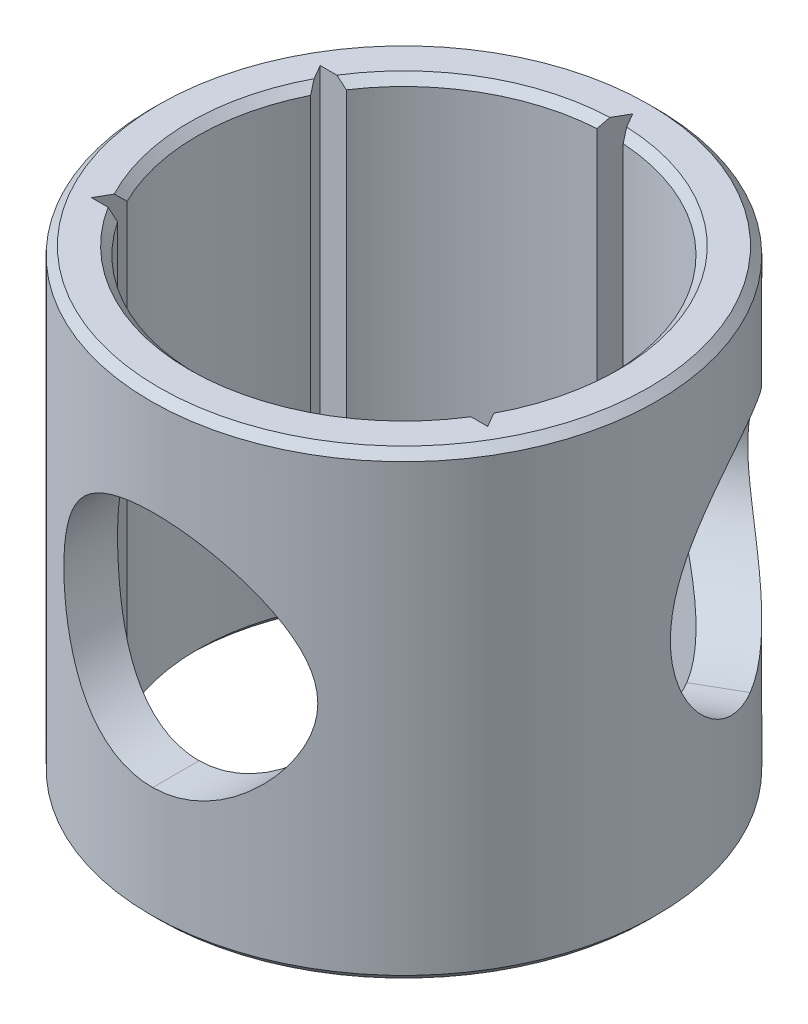
SolidWorks part; units mm, degrees
ref_plane "Ebene vorne" through (0, 0, 0) normal (0, 0, 1) x (1, 0, 0)
ref_plane "Ebene oben" through (0, 0, 0) normal (0, 1, 0) x (1, 0, 0)
ref_plane "Ebene rechts" through (0, 0, 0) normal (1, 0, 0) x (0, 0, -1)
sketch "Skizze1" plane through (0, 0, 0) normal (0, 1, 0) x (1, 0, 0)
  circle A0 centre (0, 0) radius 13
  circle A1 centre (0, 0) radius 15.925
  dimension "D1" = 26
  dimension "D2" = 31.85
extrude "Aufsatz-Linear austragen1" add sketch "Skizze1" along normal blind 29
sketch "Skizze2" plane through (0, 29, 0) normal (0, 1, 0) x (1, 0, 0)
  line L1 (0, 14.4) -> (-1.2124, 12.3)
  line L2 (-1.2124, 12.3) -> (1.2124, 12.3)
  line L3 (1.2124, 12.3) -> (0, 14.4)
  circle A0 centre (0, 13) radius 0.7 construction
  circle A1 centre (0, 0) radius 13 construction
  dimension "D1" = 1.4
extrude "Schnitt-Linear austragen1" cut sketch "Skizze2" against normal blind 30
pattern_circular "Kreismuster1" count 6 over 360 about axis through (0, 0, 0) along (0, 1, 0) skipping 3, 5 of "Schnitt-Linear austragen1"
sketch3d "3D-Skizze1"
  spline S0 degree 3 poles (-457.6373, -1653.7984, -975.9731) (-97.1864, -142.0144, -82.2273) (-28.6155, 28.5725, 16.7947) (2.1671, 22.2371, 12.8282) (2.6665, 22.0809, 12.7328) (3.606, 21.6883, 12.4992) (4.0502, 21.4519, 12.3611) (4.8934, 20.905, 12.0522) (5.2851, 20.5992, 11.884) (5.8276, 20.0999, 11.6224) (6.0012, 19.9264, 11.5335) (6.3344, 19.5649, 11.3539) (6.4946, 19.3761, 11.2628) (6.9484, 18.793, 10.9929) (7.2167, 18.3823, 10.8166) (7.6782, 17.5043, 10.494) (7.8731, 17.0307, 10.3462) (8.0761, 16.2899, 10.1874) (8.1293, 16.0372, 10.1448) (8.2016, 15.518, 10.0864) (8.2199, 15.2544, 10.0714) (8.2194, 14.7336, 10.0718) (8.2008, 14.4742, 10.0871) (8.1282, 13.9574, 10.1456) (8.0739, 13.7007, 10.1892) (7.9379, 13.2073, 10.2955) (7.8559, 12.9679, 10.3585) (7.6677, 12.5009, 10.4986) (7.5609, 12.2722, 10.576) (7.2118, 11.6092, 10.8199) (6.9431, 11.1997, 10.9962) (6.4929, 10.6219, 11.2638) (6.3348, 10.4355, 11.3537) (6.0022, 10.0747, 11.5329) (5.827, 9.8995, 11.6227) (5.2817, 9.3979, 11.8855) (4.8933, 9.0954, 12.052) (4.2697, 8.6903, 12.2808) (4.055, 8.5635, 12.3536) (3.6106, 8.3272, 12.4907) (3.3796, 8.2174, 12.5554) (2.6708, 7.9203, 12.732) (2.1818, 7.7668, 12.8258) (-21.2275, 2.9072, 15.8664) (-86.0881, 98.182, -39.1961) (1664.0012, 951.8719, -559.7226) knots -3.679496 -3.679496 -3.679496 -3.679496 0.0625 0.0625 0.125 0.125 0.1875 0.1875 0.25 0.25 0.28125 0.28125 0.3125 0.3125 0.375 0.375 0.4375 0.4375 0.46875 0.46875 0.5 0.5 0.53125 0.53125 0.5625 0.5625 0.59375 0.59375 0.625 0.625 0.6875 0.6875 0.71875 0.71875 0.75 0.75 0.8125 0.8125 0.84375 0.84375 0.875 0.875 0.9375 0.9375 3.759159 3.759159 3.759159 3.759159 only from (0.1111, 22.5, 12.9995) to (0.1111, 7.5, 12.9995) construction
  spline S1 degree 3 poles (0.1111, 22.5, 12.9995) (0.6393, 22.5, 12.995) (1.1557, 22.4452, 12.9586) (2.1671, 22.2371, 12.8282) (2.6665, 22.0809, 12.7328) (3.606, 21.6883, 12.4992) (4.0502, 21.4519, 12.3611) (4.8934, 20.905, 12.0522) (5.2851, 20.5992, 11.884) (5.8276, 20.0999, 11.6224) (6.0012, 19.9264, 11.5335) (6.3344, 19.5649, 11.3539) (6.4946, 19.3761, 11.2628) (6.9484, 18.793, 10.9929) (7.2167, 18.3823, 10.8166) (7.6782, 17.5043, 10.494) (7.8731, 17.0307, 10.3462) (8.0761, 16.2899, 10.1874) (8.1293, 16.0372, 10.1448) (8.2016, 15.518, 10.0864) (8.2199, 15.2544, 10.0714) (8.2194, 14.7336, 10.0718) (8.2008, 14.4742, 10.0871) (8.1282, 13.9574, 10.1456) (8.0739, 13.7007, 10.1892) (7.9379, 13.2073, 10.2955) (7.8559, 12.9679, 10.3585) (7.6677, 12.5009, 10.4986) (7.5609, 12.2722, 10.576) (7.2118, 11.6092, 10.8199) (6.9431, 11.1997, 10.9962) (6.4929, 10.6219, 11.2638) (6.3348, 10.4355, 11.3537) (6.0022, 10.0747, 11.5329) (5.827, 9.8995, 11.6227) (5.2817, 9.3979, 11.8855) (4.8933, 9.0954, 12.052) (4.2697, 8.6903, 12.2808) (4.055, 8.5635, 12.3536) (3.6106, 8.3272, 12.4907) (3.3796, 8.2174, 12.5554) (2.6708, 7.9203, 12.732) (2.1818, 7.7668, 12.8258) (1.1672, 7.5562, 12.9576) (0.6393, 7.5, 12.995) (0.1111, 7.5, 12.9995) knots 0 0 0 0 0.0625 0.0625 0.125 0.125 0.1875 0.1875 0.25 0.25 0.28125 0.28125 0.3125 0.3125 0.375 0.375 0.4375 0.4375 0.46875 0.46875 0.5 0.5 0.53125 0.53125 0.5625 0.5625 0.59375 0.59375 0.625 0.625 0.6875 0.6875 0.71875 0.71875 0.75 0.75 0.8125 0.8125 0.84375 0.84375 0.875 0.875 0.9375 0.9375 1 1 1 1
  spline S2 degree 3 poles (419.1015, 1299.7716, -1451.6243) (117.6658, 245.0229, -117.1146) (33.5692, 0.596, 16.6152) (-1.8468, 7.7441, 12.8773) (-2.3241, 7.8921, 12.7988) (-3.2185, 8.2722, 12.6036) (-3.6402, 8.5042, 12.4869) (-4.4351, 9.0532, 12.2272) (-4.798, 9.3633, 12.0875) (-5.2909, 9.8768, 11.8759) (-5.4469, 10.0564, 11.805) (-5.7423, 10.4328, 11.6642) (-5.8813, 10.6296, 11.5944) (-6.2658, 11.2344, 11.394) (-6.4819, 11.6606, 11.2706) (-6.7472, 12.3371, 11.1124) (-6.8261, 12.5701, 11.064) (-6.9613, 13.0431, 10.9794) (-7.0175, 13.2818, 10.9434) (-7.1527, 14.0042, 10.8559) (-7.1989, 14.4944, 10.8248) (-7.1994, 15.2434, 10.8244) (-7.1879, 15.4941, 10.8321) (-7.1425, 15.9872, 10.8621) (-7.0746, 16.475, 10.9068) (-6.9624, 16.9526, 10.9787) (-6.8276, 17.4251, 11.063) (-6.7487, 17.6588, 11.1115) (-6.483, 18.3373, 11.27) (-6.2663, 18.765, 11.3938) (-5.8802, 19.3721, 11.595) (-5.7408, 19.5692, 11.6649) (-5.4462, 19.9444, 11.8053) (-5.2906, 20.1235, 11.8761) (-4.7984, 20.6363, 12.0873) (-4.4352, 20.9467, 12.2272) (-3.6407, 21.4955, 12.4868) (-3.2201, 21.7268, 12.6031) (-2.5528, 22.0109, 12.7489) (-2.3242, 22.095, 12.7928) (-1.8541, 22.2411, 12.8693) (-1.6121, 22.3031, 12.902) (36.2667, 29.9756, 16.9146) (123.0672, -256.026, -139.4864) (372.8421, -1147.1035, -1560.664) knots -4.464251 -4.464251 -4.464251 -4.464251 0.0625 0.0625 0.125 0.125 0.1875 0.1875 0.25 0.25 0.28125 0.28125 0.3125 0.3125 0.375 0.375 0.40625 0.40625 0.4375 0.4375 0.5 0.5 0.53125 0.53125 0.5625 0.59375 0.59375 0.625 0.625 0.6875 0.6875 0.71875 0.71875 0.75 0.75 0.8125 0.8125 0.875 0.875 0.90625 0.90625 0.9375 0.9375 5.784955 5.784955 5.784955 5.784955 only from (0.1111, 7.5, 12.9995) to (0.1111, 22.5, 12.9995) construction
  spline S3 degree 3 poles (0.1111, 7.5, 12.9995) (-0.3904, 7.5, 13.0038) (-0.8821, 7.5494, 12.9791) (-1.8468, 7.7441, 12.8773) (-2.3241, 7.8921, 12.7988) (-3.2185, 8.2722, 12.6036) (-3.6402, 8.5042, 12.4869) (-4.4351, 9.0532, 12.2272) (-4.798, 9.3633, 12.0875) (-5.2909, 9.8768, 11.8759) (-5.4469, 10.0564, 11.805) (-5.7423, 10.4328, 11.6642) (-5.8813, 10.6296, 11.5944) (-6.2658, 11.2344, 11.394) (-6.4819, 11.6606, 11.2706) (-6.7472, 12.3371, 11.1124) (-6.8261, 12.5701, 11.064) (-6.9613, 13.0431, 10.9794) (-7.0175, 13.2818, 10.9434) (-7.1527, 14.0042, 10.8559) (-7.1989, 14.4944, 10.8248) (-7.1994, 15.2434, 10.8244) (-7.1879, 15.4941, 10.8321) (-7.1425, 15.9872, 10.8621) (-7.0746, 16.475, 10.9068) (-6.9624, 16.9526, 10.9787) (-6.8276, 17.4251, 11.063) (-6.7487, 17.6588, 11.1115) (-6.483, 18.3373, 11.27) (-6.2663, 18.765, 11.3938) (-5.8802, 19.3721, 11.595) (-5.7408, 19.5692, 11.6649) (-5.4462, 19.9444, 11.8053) (-5.2906, 20.1235, 11.8761) (-4.7984, 20.6363, 12.0873) (-4.4352, 20.9467, 12.2272) (-3.6407, 21.4955, 12.4868) (-3.2201, 21.7268, 12.6031) (-2.5528, 22.0109, 12.7489) (-2.3242, 22.095, 12.7928) (-1.8541, 22.2411, 12.8693) (-1.6121, 22.3031, 12.902) (-0.8842, 22.4505, 12.9791) (-0.3908, 22.5, 13.0038) (0.1111, 22.5, 12.9995) knots 0 0 0 0 0.0625 0.0625 0.125 0.125 0.1875 0.1875 0.25 0.25 0.28125 0.28125 0.3125 0.3125 0.375 0.375 0.40625 0.40625 0.4375 0.4375 0.5 0.5 0.53125 0.53125 0.5625 0.59375 0.59375 0.625 0.625 0.6875 0.6875 0.71875 0.71875 0.75 0.75 0.8125 0.8125 0.875 0.875 0.90625 0.90625 0.9375 0.9375 1 1 1 1
sketch "Skizze4" plane through (0, 0, 0) normal (0, 0, 1) x (1, 0, 0)
  spline S0 degree 3 poles (-518.1127, -1908.464) (-104.6424, -160.7971) (-30.2373, 28.9063) (2.1671, 22.2371) (2.6665, 22.0809) (3.606, 21.6883) (4.0502, 21.4519) (4.8934, 20.905) (5.2851, 20.5992) (5.8276, 20.0999) (6.0012, 19.9264) (6.3344, 19.5649) (6.4946, 19.3761) (6.9484, 18.793) (7.2167, 18.3823) (7.6782, 17.5043) (7.8731, 17.0307) (8.0761, 16.2899) (8.1293, 16.0372) (8.2016, 15.518) (8.2199, 15.2544) (8.2194, 14.7336) (8.2008, 14.4742) (8.1282, 13.9574) (8.0739, 13.7007) (7.9379, 13.2073) (7.8559, 12.9679) (7.6677, 12.5009) (7.5609, 12.2722) (7.2118, 11.6092) (6.9431, 11.1997) (6.4929, 10.6219) (6.3348, 10.4355) (6.0022, 10.0747) (5.827, 9.8995) (5.2817, 9.3979) (4.8933, 9.0954) (4.2697, 8.6903) (4.055, 8.5635) (3.6106, 8.3272) (3.3796, 8.2174) (2.6708, 7.9203) (2.1818, 7.7668) (-21.5542, 2.8394) (-87.9467, 100.9199) (1739.992, 988.8619) knots -3.879941 -3.879941 -3.879941 -3.879941 0.0625 0.0625 0.125 0.125 0.1875 0.1875 0.25 0.25 0.28125 0.28125 0.3125 0.3125 0.375 0.375 0.4375 0.4375 0.46875 0.46875 0.5 0.5 0.53125 0.53125 0.5625 0.5625 0.59375 0.59375 0.625 0.625 0.6875 0.6875 0.71875 0.71875 0.75 0.75 0.8125 0.8125 0.84375 0.84375 0.875 0.875 0.9375 0.9375 3.799401 3.799401 3.799401 3.799401 only from (0.1111, 22.5) to (0.1111, 7.5) construction
  spline S1 degree 3 poles (0.1111, 22.5) (0.6393, 22.5) (1.1557, 22.4452) (2.1671, 22.2371) (2.6665, 22.0809) (3.606, 21.6883) (4.0502, 21.4519) (4.8934, 20.905) (5.2851, 20.5992) (5.8276, 20.0999) (6.0012, 19.9264) (6.3344, 19.5649) (6.4946, 19.3761) (6.9484, 18.793) (7.2167, 18.3823) (7.6782, 17.5043) (7.8731, 17.0307) (8.0761, 16.2899) (8.1293, 16.0372) (8.2016, 15.518) (8.2199, 15.2544) (8.2194, 14.7336) (8.2008, 14.4742) (8.1282, 13.9574) (8.0739, 13.7007) (7.9379, 13.2073) (7.8559, 12.9679) (7.6677, 12.5009) (7.5609, 12.2722) (7.2118, 11.6092) (6.9431, 11.1997) (6.4929, 10.6219) (6.3348, 10.4355) (6.0022, 10.0747) (5.827, 9.8995) (5.2817, 9.3979) (4.8933, 9.0954) (4.2697, 8.6903) (4.055, 8.5635) (3.6106, 8.3272) (3.3796, 8.2174) (2.6708, 7.9203) (2.1818, 7.7668) (1.1672, 7.5562) (0.6393, 7.5) (0.1111, 7.5) knots 0 0 0 0 0.0625 0.0625 0.125 0.125 0.1875 0.1875 0.25 0.25 0.28125 0.28125 0.3125 0.3125 0.375 0.375 0.4375 0.4375 0.46875 0.46875 0.5 0.5 0.53125 0.53125 0.5625 0.5625 0.59375 0.59375 0.625 0.625 0.6875 0.6875 0.71875 0.71875 0.75 0.75 0.8125 0.8125 0.84375 0.84375 0.875 0.875 0.9375 0.9375 1 1 1 1
  spline S2 degree 3 poles (594.1635, 1916.5736) (147.9485, 336.2315) (39.5587, -0.6129) (-1.8468, 7.7441) (-2.3241, 7.8921) (-3.2185, 8.2722) (-3.6402, 8.5042) (-4.4351, 9.0532) (-4.798, 9.3633) (-5.2909, 9.8768) (-5.4469, 10.0564) (-5.7423, 10.4328) (-5.8813, 10.6296) (-6.2658, 11.2344) (-6.4819, 11.6606) (-6.7472, 12.3371) (-6.8261, 12.5701) (-6.9613, 13.0431) (-7.0175, 13.2818) (-7.1527, 14.0042) (-7.1989, 14.4944) (-7.1994, 15.2434) (-7.1879, 15.4941) (-7.1425, 15.9872) (-7.0746, 16.475) (-6.9624, 16.9526) (-6.8276, 17.4251) (-6.7487, 17.6588) (-6.483, 18.3373) (-6.2663, 18.765) (-5.8802, 19.3721) (-5.7408, 19.5692) (-5.4462, 19.9444) (-5.2906, 20.1235) (-4.7984, 20.6363) (-4.4352, 20.9467) (-3.6407, 21.4955) (-3.2201, 21.7268) (-2.5528, 22.0109) (-2.3242, 22.095) (-1.8541, 22.2411) (-1.6121, 22.3031) (45.2292, 31.791) (167.1955, -408.8905) (580.5448, -1890.8355) knots -5.240382 -5.240382 -5.240382 -5.240382 0.0625 0.0625 0.125 0.125 0.1875 0.1875 0.25 0.25 0.28125 0.28125 0.3125 0.3125 0.375 0.375 0.40625 0.40625 0.4375 0.4375 0.5 0.5 0.53125 0.53125 0.5625 0.59375 0.59375 0.625 0.625 0.6875 0.6875 0.71875 0.71875 0.75 0.75 0.8125 0.8125 0.875 0.875 0.90625 0.90625 0.9375 0.9375 6.9393 6.9393 6.9393 6.9393 only from (0.1111, 7.5) to (0.1111, 22.5) construction
  spline S3 degree 3 poles (0.1111, 7.5) (-0.3904, 7.5) (-0.8821, 7.5494) (-1.8468, 7.7441) (-2.3241, 7.8921) (-3.2185, 8.2722) (-3.6402, 8.5042) (-4.4351, 9.0532) (-4.798, 9.3633) (-5.2909, 9.8768) (-5.4469, 10.0564) (-5.7423, 10.4328) (-5.8813, 10.6296) (-6.2658, 11.2344) (-6.4819, 11.6606) (-6.7472, 12.3371) (-6.8261, 12.5701) (-6.9613, 13.0431) (-7.0175, 13.2818) (-7.1527, 14.0042) (-7.1989, 14.4944) (-7.1994, 15.2434) (-7.1879, 15.4941) (-7.1425, 15.9872) (-7.0746, 16.475) (-6.9624, 16.9526) (-6.8276, 17.4251) (-6.7487, 17.6588) (-6.483, 18.3373) (-6.2663, 18.765) (-5.8802, 19.3721) (-5.7408, 19.5692) (-5.4462, 19.9444) (-5.2906, 20.1235) (-4.7984, 20.6363) (-4.4352, 20.9467) (-3.6407, 21.4955) (-3.2201, 21.7268) (-2.5528, 22.0109) (-2.3242, 22.095) (-1.8541, 22.2411) (-1.6121, 22.3031) (-0.8842, 22.4505) (-0.3908, 22.5) (0.1111, 22.5) knots 0 0 0 0 0.0625 0.0625 0.125 0.125 0.1875 0.1875 0.25 0.25 0.28125 0.28125 0.3125 0.3125 0.375 0.375 0.40625 0.40625 0.4375 0.4375 0.5 0.5 0.53125 0.53125 0.5625 0.59375 0.59375 0.625 0.625 0.6875 0.6875 0.71875 0.71875 0.75 0.75 0.8125 0.8125 0.875 0.875 0.90625 0.90625 0.9375 0.9375 1 1 1 1
extrude "Schnitt-Linear austragen2" cut sketch "Skizze4" along normal blind 40
pattern_circular "Kreismuster2" count 2 every 120 about axis through (0, 29, 0) along (0, 1, 0) of "Schnitt-Linear austragen2"
chamfer "Fase1" distance 0.5 angle 45 10 edges at (0, 0, 13) (-13, 0, 0) (-6.5, 0, -11.2583) (11.2583, 0, -6.5) (11.2583, 29, -6.5) (-6.5, 29, -11.2583) (-13, 29, 0) (0, 29, 13) (0, 0, 15.925) (0, 29, 15.925)
